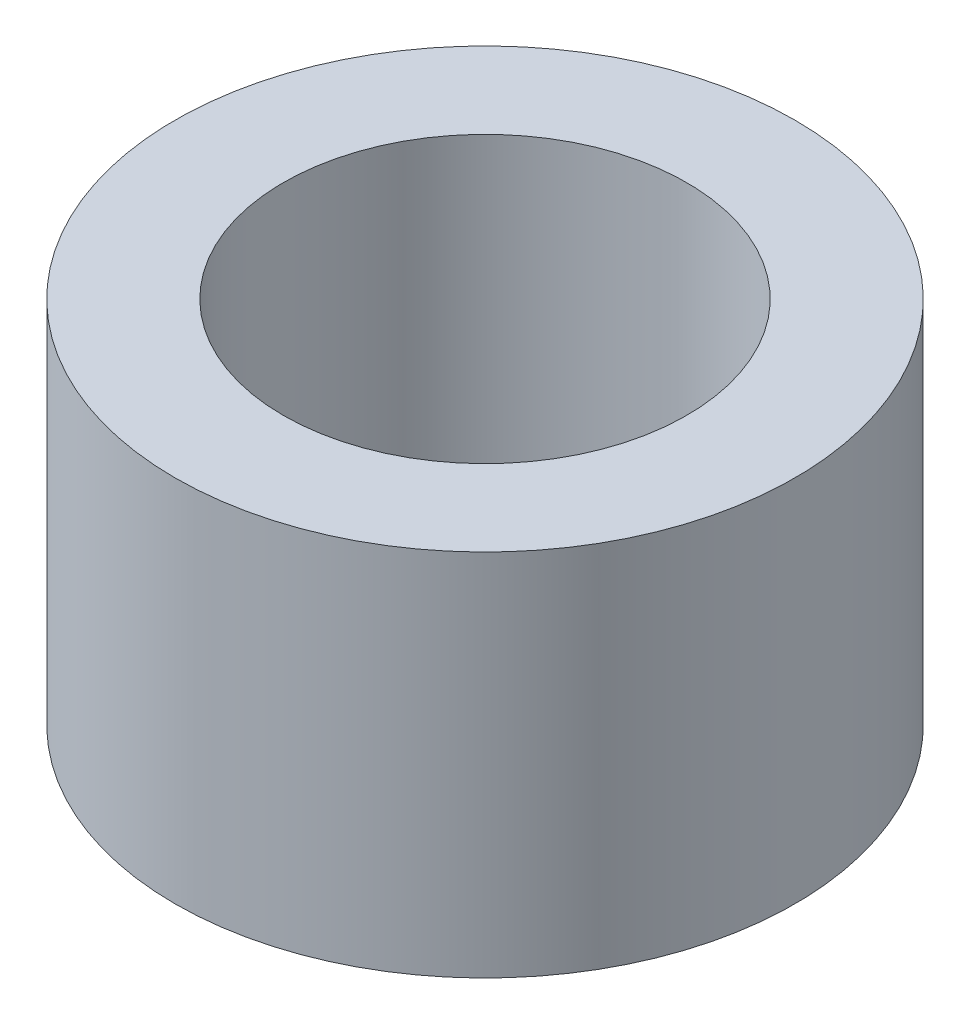
SolidWorks part; units mm, degrees
ref_plane "Alzado" through (0, 0, 0) normal (0, 0, 1) x (1, 0, 0)
ref_plane "Planta" through (0, 0, 0) normal (0, 1, 0) x (1, 0, 0)
ref_plane "Vista lateral" through (0, 0, 0) normal (1, 0, 0) x (0, 0, -1)
sketch "Croquis1" plane through (0, 0, 0) normal (0, 1, 0) x (1, 0, 0)
  circle A0 centre (0, 0) radius 4.1
  circle A1 centre (0, 0) radius 6.3
  dimension "D1" = 8.2
  dimension "D2" = 12.6
extrude "Saliente-Extruir1" add sketch "Croquis1" along normal blind 7.5
